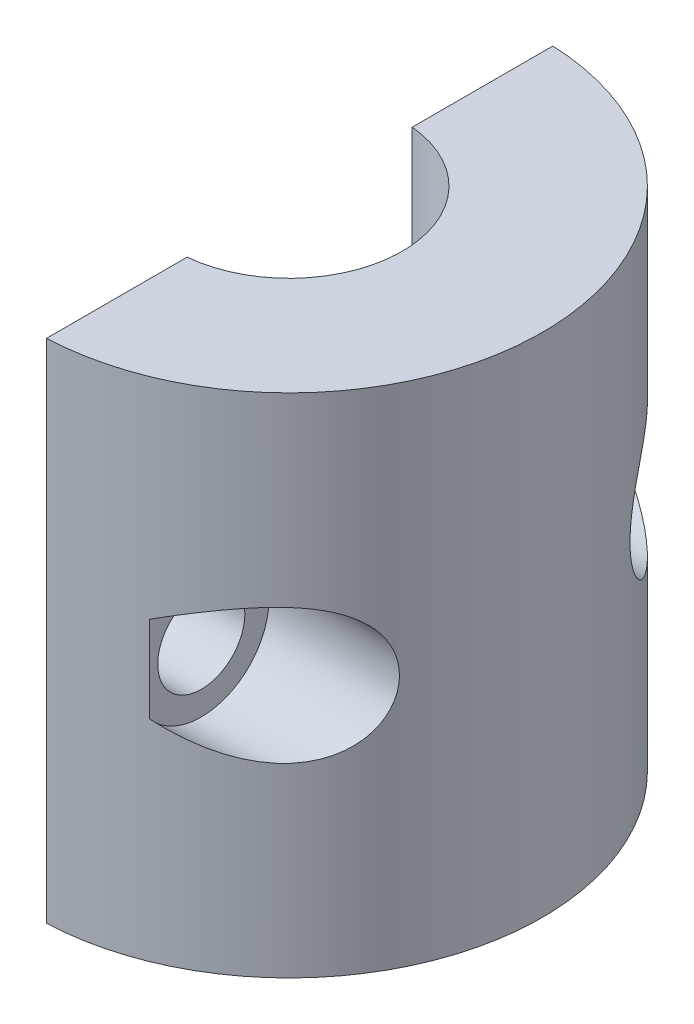
SolidWorks part; units mm, degrees
ref_plane "Front Plane" through (0, 0, 0) normal (0, 0, 1) x (1, 0, 0)
ref_plane "Top Plane" through (0, 0, 0) normal (0, 1, 0) x (1, 0, 0)
ref_plane "Right Plane" through (0, 0, 0) normal (1, 0, 0) x (0, 0, -1)
sketch "Sketch1" plane through (0, 0, 0) normal (0, 1, 0) x (1, 0, 0)
  line L0 (0.3969, 9.5167) -> (0.3969, 4.2314)
  line L1 (0.3969, -4.2314) -> (0.3969, -9.5167)
  arc A0 (0.3969, -9.5167) -> (0.3969, 9.5167) centre (0, 0) ccw
  arc A1 (0.3969, -4.2314) -> (0.3969, 4.2314) centre (0, 0) ccw
  dimension "D1" = 19.05
  dimension "D2" = 8.5
  dimension "D3" = 0.3969
extrude "Boss-Extrude1" add sketch "Sketch1" along normal blind 19.05
ref_plane "Plane1" through (3.5719, 0, 0) normal (1, 0, 0) x (0, 0, -1)
sketch "Sketch4" plane through (3.5719, 0, 0) normal (1, 0, 0) x (0, 0, -1)
  line L0 (-9.5167, 0) -> (-4.2314, 19.05) construction
  circle A0 centre (-6.8741, 9.525) radius 1.6383
  dimension "D1" = 3.2766
extrude "Cut-Extrude1" cut sketch "Sketch4" against normal through all
sketch "Sketch5" plane through (3.5719, 0, 0) normal (1, 0, 0) x (0, 0, -1)
  circle A0 centre (-6.8741, 9.525) radius 2.54
  circle A2 centre (-6.8741, 9.525) radius 1.6383 construction
  dimension "D1" = 5.08
extrude "Cut-Extrude2" cut sketch "Sketch5" along normal through all
mirror "Mirror1" about plane through (0, 0, 0) normal (0, 0, 1) of "Cut-Extrude2", "Cut-Extrude1"
